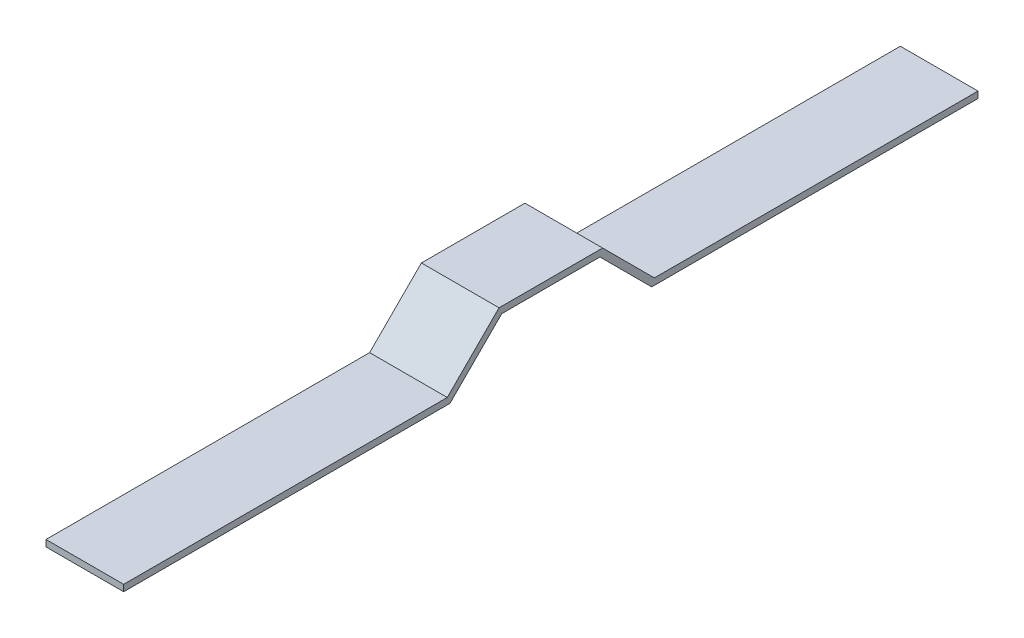
SolidWorks part; units mm, degrees
ref_plane "Front" through (0, 0, 0) normal (0, 0, 1) x (1, 0, 0)
ref_plane "Top" through (0, 0, 0) normal (0, 1, 0) x (1, 0, 0)
ref_plane "Right" through (0, 0, 0) normal (1, 0, 0) x (0, 0, -1)
sketch "Sketch1" plane through (0, 0, 0) normal (1, 0, 0) x (0, 0, -1)
  line L0 (-145.4411, -11.8301) -> (13.3089, -11.8301)
  line L1 (13.3089, -11.8301) -> (38.7089, 13.5699)
  line L2 (38.7089, 13.5699) -> (89.5089, 13.5699)
  line L3 (89.5089, 13.5699) -> (114.9089, -11.8301)
  line L4 (114.9089, -11.8301) -> (273.6589, -11.8301)
  line L5 (-145.4411, -15.0051) -> (14.624, -15.0051)
  line L6 (14.624, -15.0051) -> (40.024, 10.3949)
  line L7 (40.024, 10.3949) -> (88.1938, 10.3949)
  line L8 (88.1938, 10.3949) -> (113.5938, -15.0051)
  line L9 (113.5938, -15.0051) -> (273.6589, -15.0051)
  line L10 (-145.4411, -11.8301) -> (-145.4411, -15.0051)
  line L11 (273.6589, -15.0051) -> (273.6589, -11.8301)
  dimension "D1" = 50.8
  dimension "D2" = 25.4
  dimension "D3" = 25.4
  dimension "D4" = 158.75
  dimension "D5" = 158.75
  dimension "D6" = 25.4
  dimension "D7" = 25.4
  dimension "D8" = 3.175
extrude "Boss-Extrude1" add sketch "Sketch1" along normal blind 38.1
